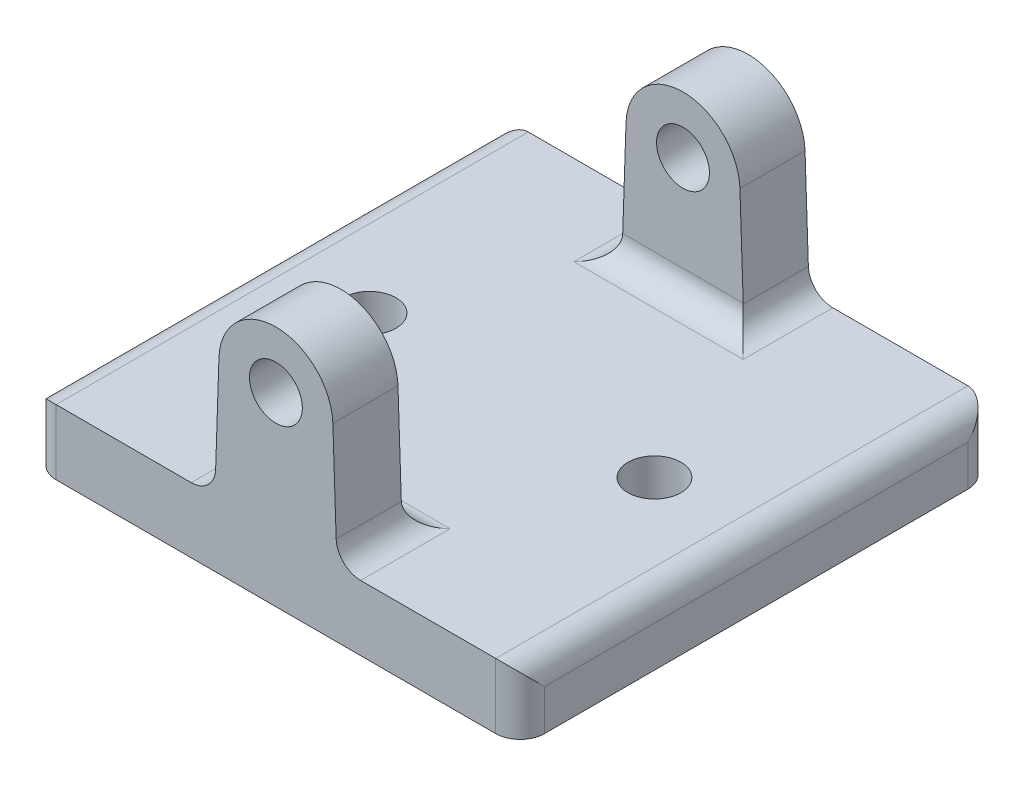
SolidWorks part; units mm, degrees
material "ABS"
ref_plane "Front Plane" through (0, 0, 0) normal (0, 0, 1) x (1, 0, 0)
ref_plane "Top Plane" through (0, 0, 0) normal (0, 1, 0) x (1, 0, 0)
ref_plane "Right Plane" through (0, 0, 0) normal (1, 0, 0) x (0, 0, -1)
sketch "Sketch2" plane through (0, 0, 0) normal (0, 1, 0) x (1, 0, 0)
  line L0 (-17.5, 0) -> (0, 0) construction
  line L1 (-30, -29) -> (30, -29)
  line L2 (-30, -29) -> (-30, 29)
  line L3 (-30, 29) -> (30, 29)
  line L4 (30, -29) -> (30, 29)
  line L5 (-30, -29) -> (30, 29) construction
  line L6 (-30, 29) -> (30, -29) construction
  line L7 (0, -55) -> (0, 55) construction
  circle A0 centre (-17.5, 0) radius 3.25
  circle A1 centre (17.5, 0) radius 3.25
  point P0 (0, 0)
  dimension "D4" = 6.5
  dimension "D1" = 58
  dimension "D2" = 60
  dimension "D3" = 17.5
extrude "Boss-Extrude1" add sketch "Sketch2" along normal blind 8
sketch "Sketch3" plane through (0, 0, 29) normal (0, 0, 1) x (1, 0, 0)
  line L0 (-7.5, 8) -> (-6.9961, 23)
  line L1 (-30, 8) -> (30, 8) construction
  line L2 (6.9961, 23) -> (7.5, 8)
  line L3 (-7.5, 8) -> (7.5, 8)
  arc A0 (-6.9961, 23) -> (6.9961, 23) centre (0, 22.765) cw
  circle A1 centre (0, 22.765) radius 3.25
  dimension "D1" = 7
  dimension "D4" = 6.5
  dimension "D2" = 15
  dimension "D3" = 15
extrude "Boss-Extrude2" add sketch "Sketch3" against normal blind 8
mirror "Mirror1" about plane through (0, 0, 0) normal (0, 0, 1) of "Boss-Extrude2"
fillet "Fillet1" radius 3 12 edges at (7.5, 8, -25) (7.5, 8, 25) (-7.5, 8, 25) (-7.5, 8, -25) (30, 8, 0) (0, 8, 21) (-30, 8, 0) (0, 8, -21) (30, 4, 29) (-30, 4, 29) (-30, 4, -29) (30, 4, -29)
